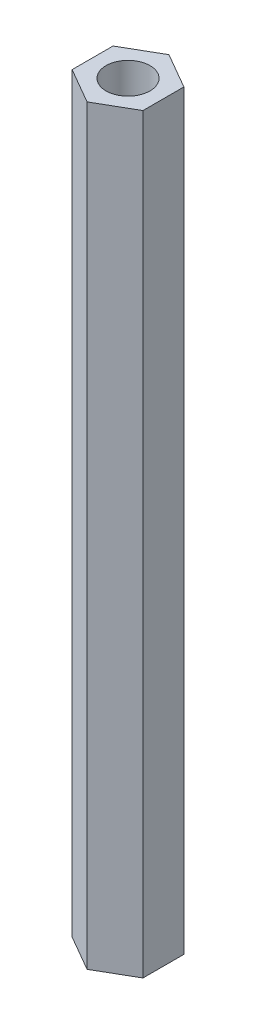
SolidWorks part; units mm, degrees
material "Простая углеродистая сталь"
ref_plane "Спереди" through (0, 0, 0) normal (0, 0, 1) x (1, 0, 0)
ref_plane "Сверху" through (0, 0, 0) normal (0, 1, 0) x (1, 0, 0)
ref_plane "Справа" through (0, 0, 0) normal (1, 0, 0) x (0, 0, -1)
sketch "Эскиз1" plane through (0, 0, 0) normal (0, 1, 0) x (1, 0, 0)
  line L0 (0, 0) -> (0, 2.8868) construction
  line L1 (0, -2.8868) -> (2.5, -1.4434)
  line L2 (2.5, -1.4434) -> (2.5, 1.4434)
  line L3 (2.5, 1.4434) -> (0, 2.8868)
  line L4 (0, 2.8868) -> (-2.5, 1.4434)
  line L5 (-2.5, 1.4434) -> (-2.5, -1.4434)
  line L6 (-2.5, -1.4434) -> (0, -2.8868)
  circle A0 centre (0, 0) radius 2.5 construction
  circle A1 centre (0, 0) radius 1.55
  dimension "D2" = 3.1
  dimension "D1" = 5
extrude "Бобышка-Вытянуть1" add sketch "Эскиз1" along normal blind 53
